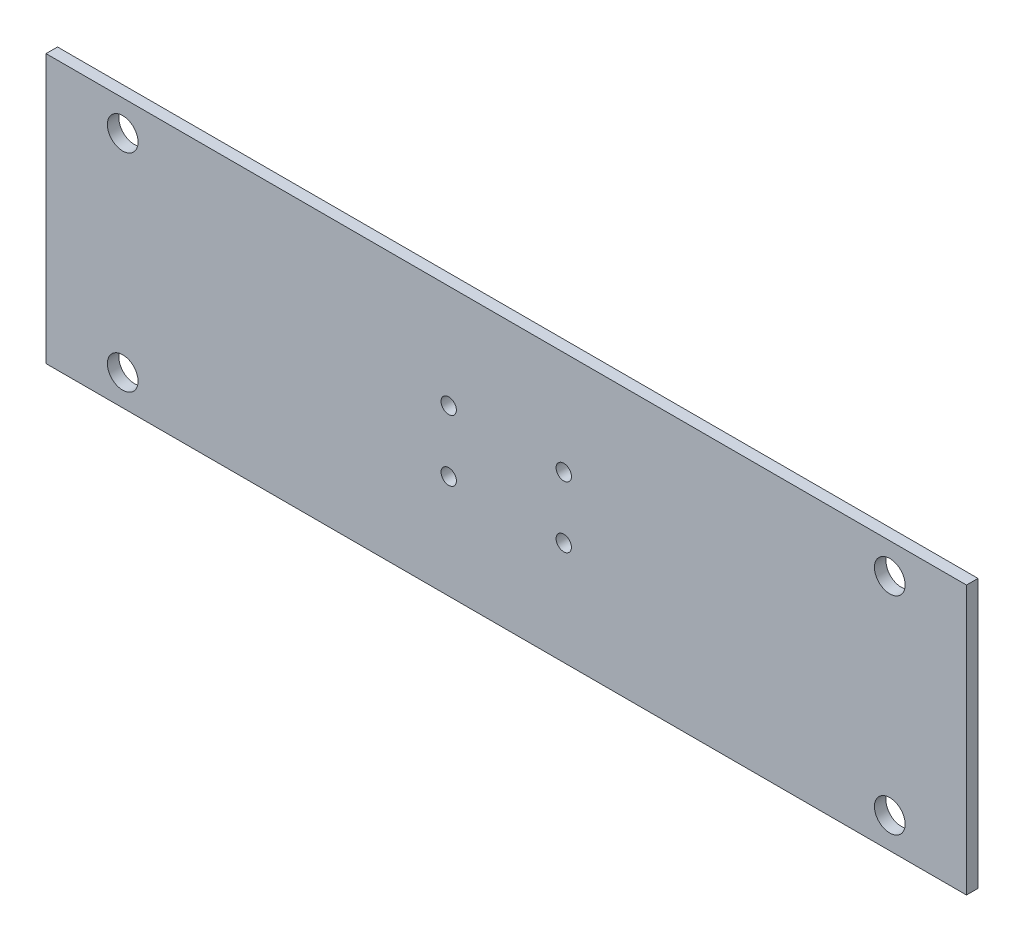
SolidWorks part; units mm, degrees
material "AISI 316 Stainless Steel Sheet (SS)"
ref_plane "Front Plane" through (0, 0, 0) normal (0, 0, 1) x (1, 0, 0)
ref_plane "Top Plane" through (0, 0, 0) normal (0, 1, 0) x (1, 0, 0)
ref_plane "Right Plane" through (0, 0, 0) normal (1, 0, 0) x (0, 0, -1)
sketch "Sketch1" plane through (0, 0, 0) normal (0, 0, 1) x (1, 0, 0)
  line L0 (0, -35) -> (0, 35) construction
  line L1 (-120, -35) -> (120, -35)
  line L2 (-120, -35) -> (-120, 35)
  line L3 (-120, 35) -> (120, 35)
  line L4 (120, -35) -> (120, 35)
  line L5 (-120, -35) -> (120, 35) construction
  line L6 (-120, 35) -> (120, -35) construction
  line L7 (-120, 0) -> (120, 0) construction
  circle A0 centre (-100, 27) radius 4
  circle A1 centre (100, 27) radius 4
  circle A2 centre (100, -27) radius 4
  circle A3 centre (-100, -27) radius 4
  circle A4 centre (-15, 8) radius 2
  circle A5 centre (15, 8) radius 2
  circle A6 centre (15, -8) radius 2
  circle A7 centre (-15, -8) radius 2
  point P0 (0, 0)
  dimension "D3" = 8
  dimension "D6" = 4
  dimension "D1" = 70
  dimension "D2" = 240
  dimension "D4" = 20
  dimension "D5" = 8
  dimension "D7" = 15
  dimension "D8" = 8
extrude "Boss-Extrude1" add sketch "Sketch1" along normal blind 3
